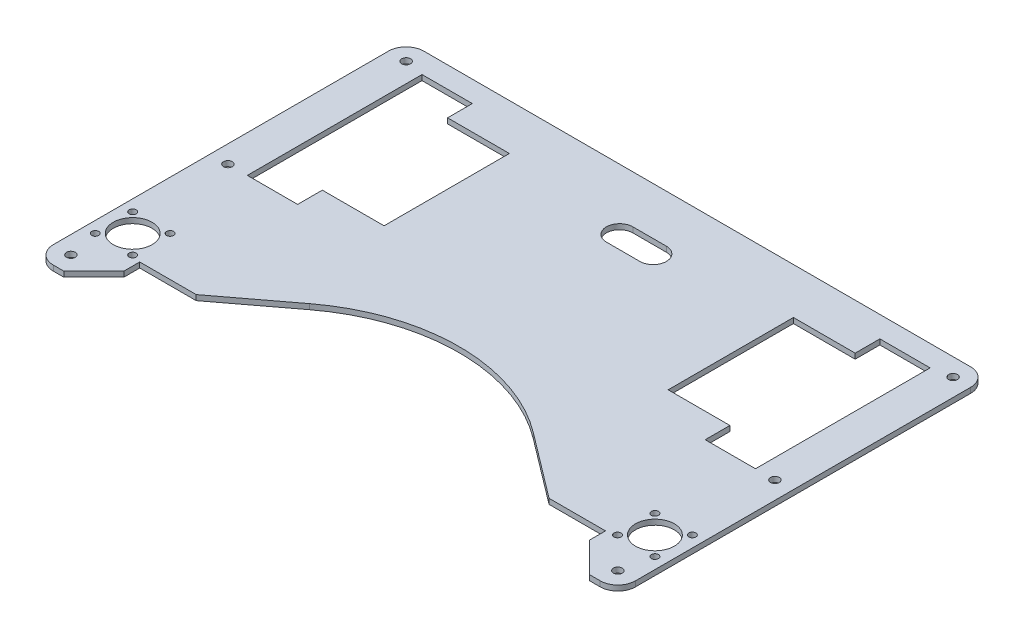
SolidWorks part; units mm, degrees
ref_plane "Face" through (0, 0, 0) normal (0, 0, 1) x (1, 0, 0)
ref_plane "Dessus" through (0, 0, 0) normal (0, 1, 0) x (1, 0, 0)
ref_plane "Droite" through (0, 0, 0) normal (1, 0, 0) x (0, 0, -1)
sketch "Esquisse1" plane through (0, 0, 0) normal (0, 1, 0) x (1, 0, 0)
  line L0 (165, 0) -> (-165, 0)
  line L1 (-165, 0) -> (-165, -210)
  line L2 (-165, -210) -> (-149, -210)
  line L3 (0, 0) -> (0, -240) construction
  line L4 (-165, -210) -> (165, -210) construction
  line L5 (-80.5, -26) -> (-115.5, -26)
  line L6 (-144, -12) -> (-144, -111)
  line L7 (-115.5, -26) -> (-115.5, -12)
  line L8 (-80.5, -26) -> (-80.5, -97)
  line L9 (115.5, -26) -> (115.5, -12)
  line L10 (115.5, -12) -> (144, -12)
  line L11 (80.5, -26) -> (115.5, -26)
  line L12 (80.5, -26) -> (80.5, -97)
  line L13 (80.5, -97) -> (115.5, -97)
  line L14 (165, -210) -> (149, -210)
  line L15 (165, 0) -> (165, -210)
  line L16 (-148, -161) -> (-148, -183) construction
  line L17 (-132, -184) -> (-132, -193)
  line L18 (-132, -184) -> (-100, -184)
  line L19 (-159, -172) -> (-137, -172) construction
  line L20 (-148, -172) -> (-159, -161) construction
  line L21 (-159, -172) -> (-159, -161) construction
  line L22 (-159, -161) -> (-148, -161) construction
  line L23 (-63.3633, -156.2737) -> (-100, -184)
  line L24 (-165, -159) -> (-66.9657, -159) construction
  line L25 (132, -184) -> (100, -184)
  line L26 (132, -184) -> (132, -193)
  line L27 (63.3633, -156.2737) -> (100, -184)
  line L28 (-149, -210) -> (-132, -193)
  line L29 (-115.5, -12) -> (-144, -12)
  line L30 (-80.5, -97) -> (-115.5, -97)
  line L31 (-115.5, -97) -> (-115.5, -111)
  line L32 (-115.5, -111) -> (-144, -111)
  line L33 (115.5, -97) -> (115.5, -111)
  line L34 (115.5, -111) -> (144, -111)
  line L35 (144, -12) -> (144, -111)
  line L36 (149, -210) -> (132, -193)
  line L37 (-137, -172) -> (-125, -172) construction
  line L38 (-144, -111) -> (-165, -111) construction
  line L39 (-80.5, -26) -> (80.5, -26) construction
  line L41 (9.5, -27) -> (-9.5, -27)
  line L42 (-9.5, -42) -> (9.5, -42)
  arc A0 (-63.3633, -156.2737) -> (63.3633, -156.2737) centre (0, -240) cw
  circle A1 centre (-155, -10) radius 2.5
  circle A2 centre (155, -10) radius 2.5
  circle A3 centre (-155, -200) radius 2.5
  circle A4 centre (155, -200) radius 2.5
  circle A5 centre (-148, -172) radius 11
  circle A6 centre (-158.6066, -161.3934) radius 2
  circle A7 centre (-137.3934, -161.3934) radius 2
  circle A8 centre (-137.3934, -182.6066) radius 2
  circle A9 centre (-158.6066, -182.6066) radius 2
  circle A10 centre (148, -172) radius 11
  circle A11 centre (158.6066, -182.6066) radius 2
  circle A12 centre (137.3934, -182.6066) radius 2
  circle A13 centre (137.3934, -161.3934) radius 2
  circle A14 centre (158.6066, -161.3934) radius 2
  circle A15 centre (-155, -111) radius 2.5
  circle A16 centre (155, -111) radius 2.5
  arc A17 (-9.5, -27) -> (-9.5, -42) centre (-9.5, -34.5) ccw
  arc A18 (9.5, -27) -> (9.5, -42) centre (9.5, -34.5) cw
  point P79 (-17, -34.5)
  point P82 (0, -27)
  point P83 (0, -42)
  dimension "D3" = 32
  dimension "D9" = 5
  dimension "D10" = 105
  dimension "D13" = 5
  dimension "D16" = 22
  dimension "D18" = 4
  dimension "D25" = 17
  dimension "D27" = 23
  dimension "D29" = 5
  dimension "D33" = 1
  dimension "D1" = 165
  dimension "D2" = 210
  dimension "D4" = 26
  dimension "D5" = 14
  dimension "D6" = 80.5
  dimension "D7" = 21
  dimension "D8" = 71
  dimension "D11" = 10
  dimension "D12" = 10
  dimension "D14" = 10
  dimension "D15" = 10
  dimension "D17" = 17
  dimension "D19" = 15
  dimension "D20" = 38
  dimension "D21" = 26
  dimension "D22" = 25
  dimension "D23" = 45
  dimension "D24" = 35
  dimension "D26" = 23
  dimension "D28" = 30
  dimension "D30" = 10
  dimension "D31" = 17
  dimension "D32" = 15
extrude "Extrusion1" add sketch "Esquisse1" along normal blind 3
fillet "Congé1" radius 10 4 edges at (-165, 1.5, 210) (165, 1.5, 210) (165, 1.5, 0) (-165, 1.5, 0)
